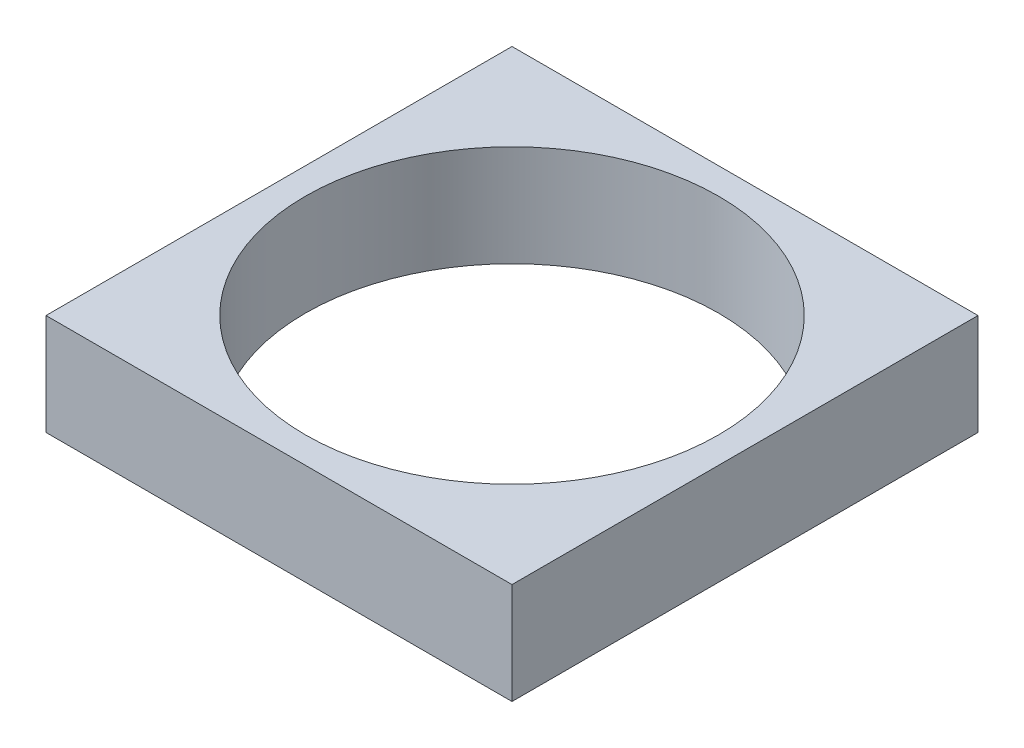
SolidWorks part; units mm, degrees
ref_plane "Front Plane" through (0, 0, 0) normal (0, 0, 1) x (1, 0, 0)
ref_plane "Top Plane" through (0, 0, 0) normal (0, 1, 0) x (1, 0, 0)
ref_plane "Right Plane" through (0, 0, 0) normal (1, 0, 0) x (0, 0, -1)
sketch "Sketch1" plane through (0, 0, 0) normal (0, 1, 0) x (1, 0, 0)
  line L1 (-11.5, -11.5) -> (11.5, -11.5)
  line L2 (-11.5, -11.5) -> (-11.5, 11.5)
  line L3 (-11.5, 11.5) -> (11.5, 11.5)
  line L4 (11.5, -11.5) -> (11.5, 11.5)
  line L5 (-11.5, -11.5) -> (11.5, 11.5) construction
  line L6 (-11.5, 11.5) -> (11.5, -11.5) construction
  circle A1 centre (0, 0) radius 10.2
  point P0 (0, 0)
  dimension "D2" = 20.4
  dimension "D1" = 23
extrude "Boss-Extrude1" add sketch "Sketch1" along normal mid plane 5
